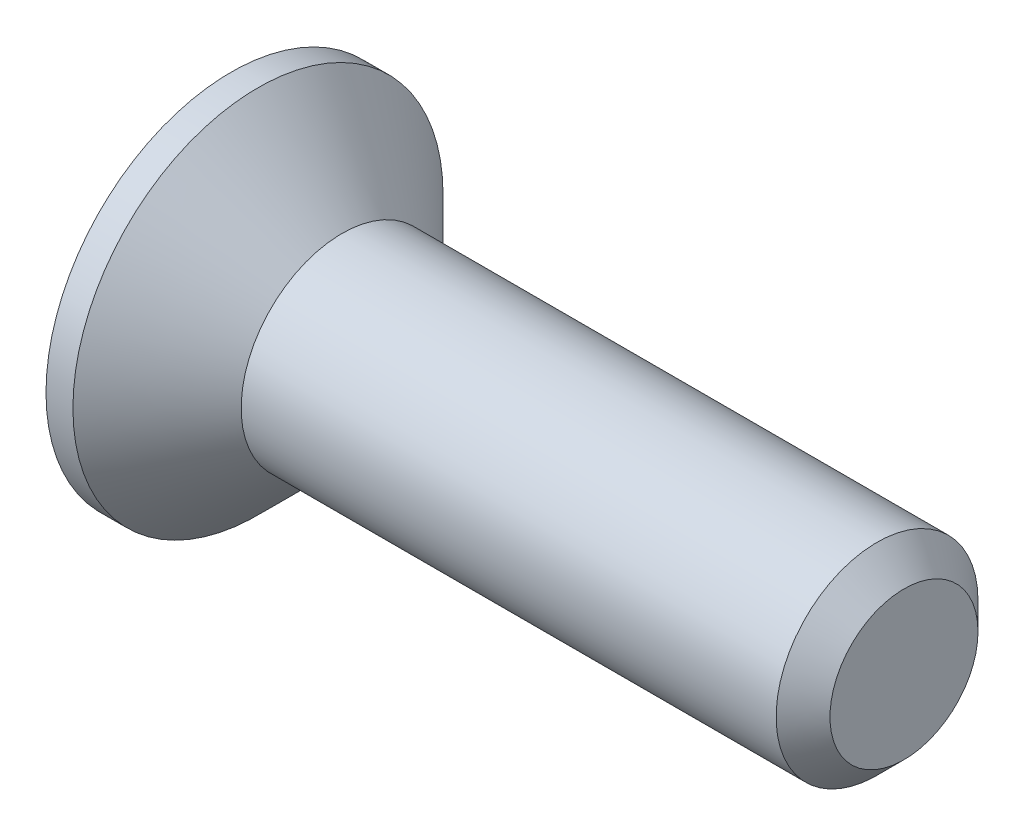
SolidWorks part; units mm, degrees
ref_plane "Front Plane" through (0, 0, 0) normal (0, 0, 1) x (1, 0, 0)
ref_plane "Top Plane" through (0, 0, 0) normal (0, 1, 0) x (1, 0, 0)
ref_plane "Right Plane" through (0, 0, 0) normal (1, 0, 0) x (0, 0, -1)
sketch "Sketch1" plane through (0, 0, 0) normal (0, 0, 1) x (1, 0, 0)
  line L0 (-4.2127, 1.5) -> (-5.4627, 2.75)
  line L1 (-4.2127, 1.5) -> (3.7373, 1.5)
  line L5 (-5.4627, 2.75) -> (-5.8627, 2.75)
  line L6 (-5.8627, 2.75) -> (-5.8627, 0)
  line L8 (3.7373, 1.5) -> (4.1373, 1.1)
  line L9 (4.1373, 1.1) -> (4.1373, 0)
  line L12 (48.1848, 0) -> (-45.0899, 0) construction
  line L13 (-5.8627, 0) -> (4.1373, 0)
  dimension "D1" = 135
  dimension "D2" = 10
  dimension "D3" = 1.65
  dimension "D4" = 0.4
  dimension "D5" = 135
  dimension "D6" = 2.75
  dimension "D7" = 1.5
revolve "Revolve1" add sketch "Sketch1" angle 360 about L12
sketch "Sketch2" plane through (-5.8627, 0, 0) normal (-1, 0, 0) x (0, 0, 1)
  line L0 (3.3657, 0) -> (-4.2952, 0) construction
  line L1 (-3.1541, -1.821) -> (3.9039, 2.2539) construction
  arc A1 (1.1666, 0.3446) -> (0.8817, 0.838) centre (0.9566, 0.5523) ccw
  circle A2 centre (0, 0) radius 1.025
  arc A3 (1.1666, 0.3446) -> (1.1666, -0.3446) centre (1.515, 0) ccw
  arc A4 (0.8817, -0.838) -> (0.2849, -1.1826) centre (0.7575, -1.312) ccw
  arc A5 (0.8817, -0.838) -> (1.1666, -0.3446) centre (0.9566, -0.5523) ccw
  arc A6 (-0.2849, -1.1826) -> (-0.8817, -0.838) centre (-0.7575, -1.312) ccw
  arc A7 (-0.2849, -1.1826) -> (0.2849, -1.1826) centre (0, -1.1046) ccw
  arc A8 (-1.1666, -0.3446) -> (-1.1666, 0.3446) centre (-1.515, 0) ccw
  arc A9 (-1.1666, -0.3446) -> (-0.8817, -0.838) centre (-0.9566, -0.5523) ccw
  arc A10 (-0.8817, 0.838) -> (-0.2849, 1.1826) centre (-0.7575, 1.312) ccw
  arc A11 (-0.8817, 0.838) -> (-1.1666, 0.3446) centre (-0.9566, 0.5523) ccw
  arc A12 (0.2849, 1.1826) -> (0.8817, 0.838) centre (0.7575, 1.312) ccw
  arc A13 (0.2849, 1.1826) -> (-0.2849, 1.1826) centre (0, 1.1046) ccw
  circle A15 centre (0, 0) radius 1.4 construction
  point P35 (0, 0)
  dimension "D1" = 2.8
  dimension "D2" = 2.05
  dimension "D3" = 0.98
  dimension "D4" = 30
  dimension "D6" = 6
extrude "Cut-Extrude1" cut sketch "Sketch2" against normal blind 0.83 contours A12 A1 A3 A5 A4 A7 A6 A9 A8 A11 A10 A13
chamfer "Chamfer2" distance 0.05 angle 45 12 edges at (-5.8627, -0.8877, 0.5125) (-5.8627, -1.4, 0) (-5.8627, -0.7, 1.2124) (-5.8627, -0.8877, -0.5125) (-5.8627, 0, 1.025) (-5.8627, -0.7, -1.2124) (-5.8627, 0.7, 1.2124) (-5.8627, 0, -1.025) (-5.8627, 0.8877, 0.5125) (-5.8627, 0.7, -1.2124) (-5.8627, 1.4, 0) (-5.8627, 0.8877, -0.5125)
